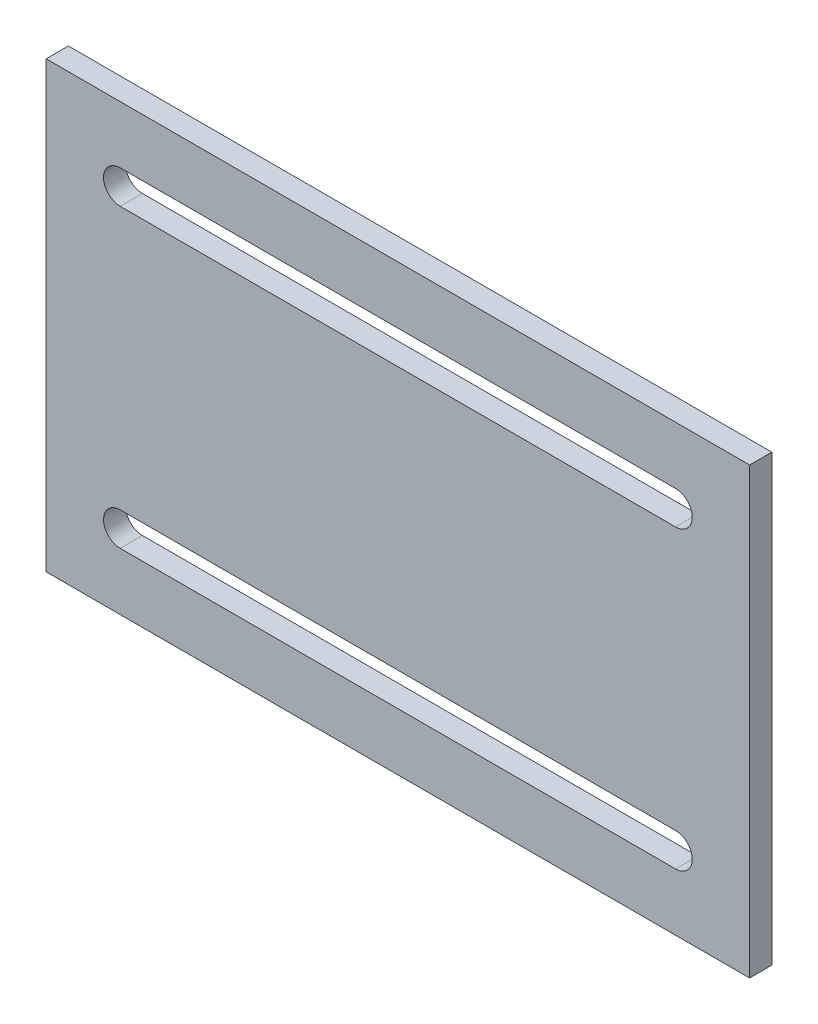
SolidWorks part; units mm, degrees
material "Plain Carbon Steel"
ref_plane "Front Plane" through (0, 0, 0) normal (0, 0, 1) x (1, 0, 0)
ref_plane "Top Plane" through (0, 0, 0) normal (0, 1, 0) x (1, 0, 0)
ref_plane "Right Plane" through (0, 0, 0) normal (1, 0, 0) x (0, 0, -1)
sketch "Sketch1" plane through (0, 0, 0) normal (0, 0, 1) x (1, 0, 0)
  line L0 (-190, -120) -> (190, -120)
  line L1 (-190, -120) -> (-190, 120)
  line L2 (190, -120) -> (190, 120)
  line L3 (-190, 120) -> (190, 120)
  line L4 (-190, -120) -> (190, 120) construction
  line L5 (190, -120) -> (-190, 120) construction
  line L6 (-190, 0) -> (190, 0) construction
  line L7 (-150, 80) -> (150, 80) construction
  line L8 (-150, 89) -> (150, 89)
  line L9 (-150, 71) -> (150, 71)
  line L10 (-150, -80) -> (150, -80) construction
  line L11 (-150, -89) -> (150, -89)
  line L12 (-150, -71) -> (150, -71)
  arc A0 (-150, 89) -> (-150, 71) centre (-150, 80) ccw
  arc A1 (150, 71) -> (150, 89) centre (150, 80) ccw
  arc A2 (-150, -89) -> (-150, -71) centre (-150, -80) cw
  arc A3 (150, -71) -> (150, -89) centre (150, -80) cw
  point P1 (0, 0)
  point P10 (0, 80)
  point P17 (0, -80)
  dimension "D1" = 380
  dimension "D2" = 240
  dimension "D3" = 18
  dimension "D4" = 80
  dimension "D5" = 40
  dimension "D6" = 40
extrude "Boss-Extrude1" add sketch "Sketch1" along normal blind 12
